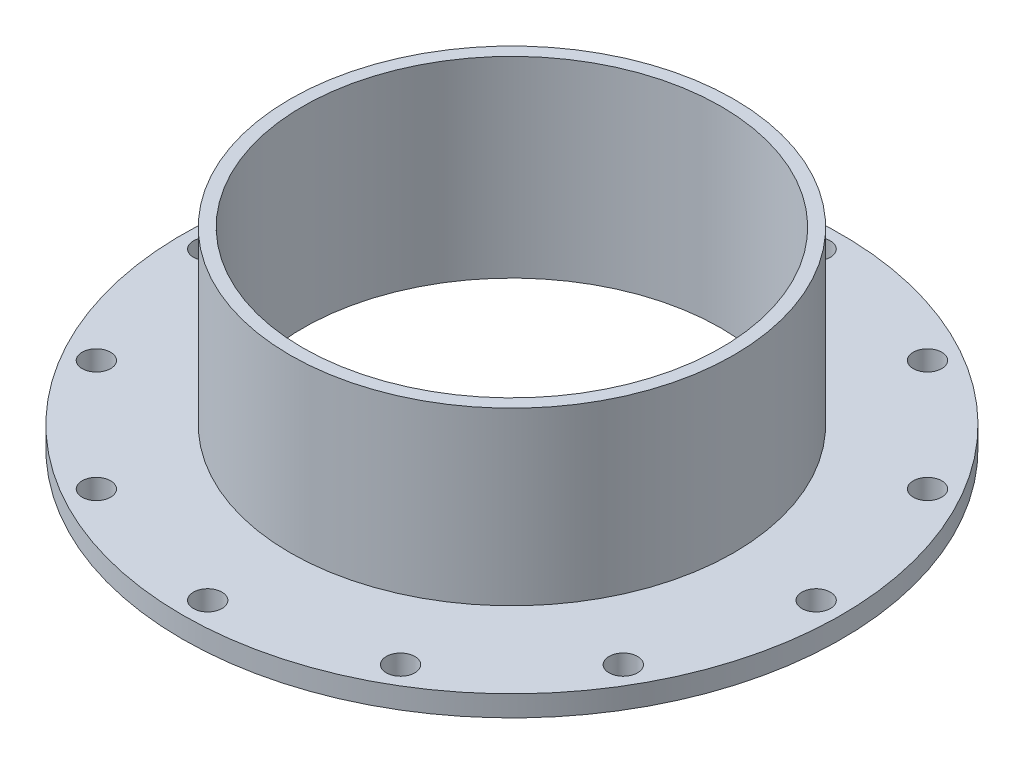
SolidWorks part; units mm, degrees
ref_plane "Front Plane" through (0, 0, 0) normal (0, 0, 1) x (1, 0, 0)
ref_plane "Top Plane" through (0, 0, 0) normal (0, 1, 0) x (1, 0, 0)
ref_plane "Right Plane" through (0, 0, 0) normal (1, 0, 0) x (0, 0, -1)
sketch "Sketch1" plane through (0, 0, 0) normal (0, 1, 0) x (1, 0, 0)
  circle A0 centre (0, 0) radius 52
  circle A1 centre (0, 0) radius 33
  dimension "D1" = 104
  dimension "D2" = 66
extrude "Boss-Extrude1" add sketch "Sketch1" along normal blind 3.3
sketch "Sketch2" plane through (0, 3.3, 0) normal (0, 1, 0) x (1, 0, 0)
  circle A0 centre (0, 0) radius 35
  circle A1 centre (0, 0) radius 33
  dimension "D1" = 70
extrude "Boss-Extrude2" add sketch "Sketch2" along normal blind 27
sketch "Sketch3" plane through (0, 3.3, 0) normal (0, 1, 0) x (1, 0, 0)
  circle A0 centre (0, 48) radius 2.25
  dimension "D1" = 4.5
  dimension "D2" = 48
extrude "Cut-Extrude1" cut sketch "Sketch3" against normal through all
pattern_circular "CirPattern1" count 12 over 360 about axis through (0, 0, 0) along (0, 1, 0) of "Cut-Extrude1"
